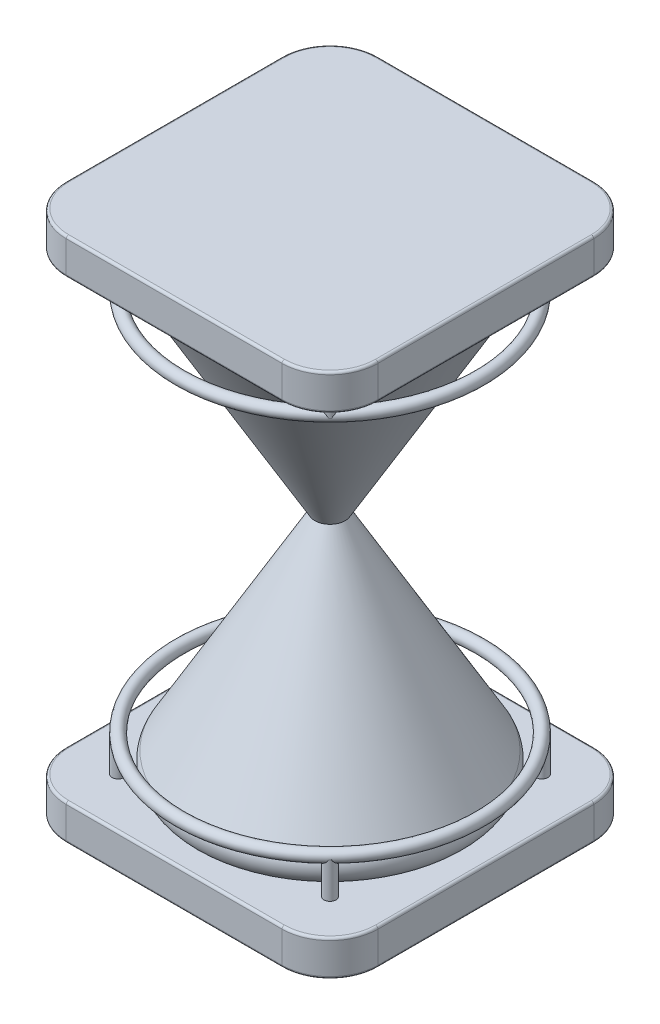
SolidWorks part; units mm, degrees
material "1060 Alloy"
ref_plane "Front Plane" through (0, 0, 0) normal (0, 0, 1) x (1, 0, 0)
ref_plane "Top Plane" through (0, 0, 0) normal (0, 1, 0) x (1, 0, 0)
ref_plane "Right Plane" through (0, 0, 0) normal (1, 0, 0) x (0, 0, -1)
sketch "Sketch1" plane through (0, 0, 0) normal (0, 0, 1) x (1, 0, 0)
  line L0 (0, 0) -> (127, 0)
  line L1 (137.9985, 19.05) -> (10.16, 240.4728)
  line L2 (0, 374.2822) -> (0, -175.1007) construction
  arc A0 (127, 0) -> (137.9985, 19.05) centre (127, 12.7) ccw
  point P8 (0, 374.2822)
  dimension "D1" = 12.7
  dimension "D2" = 127
  dimension "D3" = 60
  dimension "D4" = 10.16
revolve "Revolve-Thin1" add sketch "Sketch1" angle 360 about L2
sketch "Sketch2" plane through (0, 0, 0) normal (0, 1, 0) x (1, 0, 0)
  line L0 (-165.1, 165.1) -> (165.1, -165.1) construction
  line L1 (-165.1, 165.1) -> (165.1, 165.1)
  line L2 (-165.1, 165.1) -> (-165.1, -165.1)
  line L3 (-165.1, -165.1) -> (165.1, -165.1)
  line L4 (165.1, 165.1) -> (165.1, -165.1)
  line L5 (165.1, 165.1) -> (-165.1, -165.1) construction
  dimension "D1" = 330.2
  dimension "D2" = 0
  dimension "D3" = 0
  dimension "D4" = 330.2
extrude "Boss-Extrude1" add sketch "Sketch2" against normal blind 38.1 separate body
fillet "Fillet1" radius 50.8 4 edges at (165.1, -19.05, 165.1) (165.1, -19.05, -165.1) (-165.1, -19.05, -165.1) (-165.1, -19.05, 165.1)
fillet "Fillet2" radius 2.54 16 edges at (150.221, -38.1, 150.221) (0, -38.1, 165.1) (-150.221, -38.1, 150.221) (-165.1, -38.1, 0) (-150.221, -38.1, -150.221) (0, -38.1, -165.1) (150.221, -38.1, -150.221) (150.221, 0, 150.221) (0, 0, 165.1) (-150.221, 0, 150.221) (-165.1, 0, 0) (-150.221, 0, -150.221) (0, 0, -165.1) (150.221, 0, -150.221) (165.1, -38.1, 0) (165.1, 0, 0)
sketch "Sketch3" plane through (0, 0, 0) normal (0, 1, 0) x (1, 0, 0)
  line L0 (-243.526, 0) -> (259.9139, 0) construction
  line L1 (0, 191.0168) -> (0, -218.8793) construction
  line L2 (-112.2532, 112.2532) -> (0, 0) construction
  circle A0 centre (-112.2532, 112.2532) radius 6.35
  circle A1 centre (112.2532, 112.2532) radius 6.35
  circle A2 centre (112.2532, -112.2532) radius 6.35
  circle A3 centre (-112.2532, -112.2532) radius 6.35
  dimension "D1" = 12.7
  dimension "D2" = 158.75
  dimension "D3" = 45
extrude "Boss-Extrude2" add sketch "Sketch3" along normal blind 38.1
sketch "Sketch4" plane through (0, 38.1, 0) normal (0, 1, 0) x (1, 0, 0)
  circle A0 centre (0, 0) radius 158.75
sweep "Sweep1" add path "Sketch4" circular profile diameter 12.7 parameters "D3"=12.7
ref_plane "Plane1" through (0, 240.4728, 0) normal (0, -1, 0) x (-1, 0, 0)
mirror "Mirror2" about plane through (0, 240.4728, 0) normal (0, -1, 0) of bodies 102 101 104 106 103 108 107
